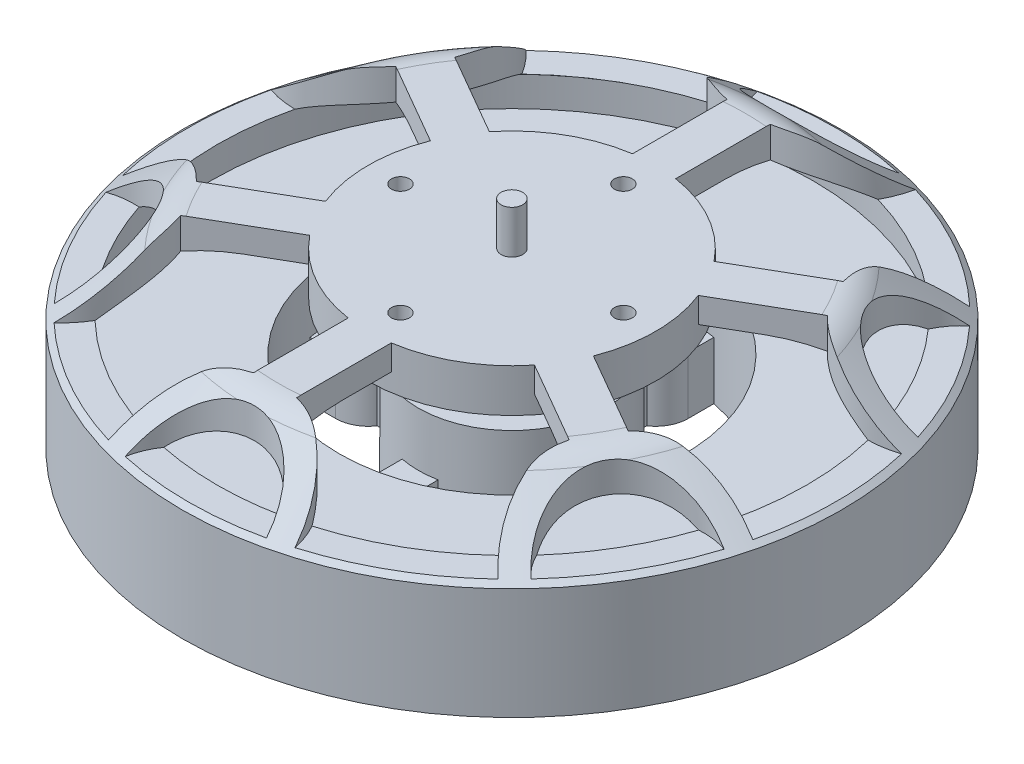
SolidWorks part; units mm, degrees
ref_plane "Front Plane" through (0, 0, 0) normal (0, 0, 1) x (1, 0, 0)
ref_plane "Top Plane" through (0, 0, 0) normal (0, 1, 0) x (1, 0, 0)
ref_plane "Right Plane" through (0, 0, 0) normal (1, 0, 0) x (0, 0, -1)
ref_plane "Plane1" through (0, 0, 0) normal (-0.7071, 0, 0.7071) x (0.7071, 0, 0.7071)
ref_axis "Axis1" through (0, 40.089, 0) along (0, -1, 0)
sketch "Sketch1" plane through (0, 0, 0) normal (0, 0, 1) x (1, 0, 0)
  line L0 (0, 0) -> (9.65, 0)
  line L1 (9.65, 0) -> (9.65, 3.93)
  line L2 (9.65, 3.93) -> (27.5, 3.93)
  line L3 (27.5, 3.93) -> (45.83, 8.08)
  line L4 (45.83, 8.08) -> (45.83, 23.58)
  line L5 (45.83, 23.58) -> (36.1322, 30.9557)
  line L6 (32.5, 32.18) -> (1.5, 32.18)
  line L7 (1.5, 32.18) -> (1.5, 38.18)
  line L8 (1.5, 38.18) -> (0, 38.18)
  line L9 (0, 38.18) -> (0, 0) construction
  line L10 (0, 0) -> (0, 38.18)
  arc A0 (36.1322, 30.9557) -> (32.5, 32.18) centre (32.5, 26.18) ccw
  dimension "D10" = 6
  dimension "D1" = 3
  dimension "D2" = 6
  dimension "D3" = 28.25
  dimension "D4" = 3.93
  dimension "D5" = 19.3
  dimension "D6" = 4.15
  dimension "D7" = 91.66
  dimension "D8" = 55
  dimension "D9" = 65
  dimension "D11" = 15.5
revolve "Revolve1" add sketch "Sketch1" angle 360 about L9
sketch "Sketch2" plane through (0, 3.93, 0) normal (0, -1, 0) x (1, 0, 0)
  line L0 (0, 0) -> (0, 27.5) construction
  line L1 (2.5, 12.7574) -> (2.5, 16.2583)
  line L2 (4.5, 20) -> (4.5, 23.5744)
  line L3 (0, 0) -> (16.9706, 16.9706) construction
  line L4 (20, 4.5) -> (23.5744, 4.5)
  line L5 (12.7574, 2.5) -> (16.2583, 2.5)
  line L6 (20, -4.5) -> (23.5744, -4.5)
  line L7 (4.5, -20) -> (4.5, -23.5744)
  line L8 (2.5, -12.7574) -> (2.5, -16.2583)
  line L9 (12.7574, -2.5) -> (16.2583, -2.5)
  line L10 (-4.5, -20) -> (-4.5, -23.5744)
  line L11 (-20, -4.5) -> (-23.5744, -4.5)
  line L12 (-12.7574, -2.5) -> (-16.2583, -2.5)
  line L13 (-2.5, -12.7574) -> (-2.5, -16.2583)
  line L14 (-20, 4.5) -> (-23.5744, 4.5)
  line L15 (-4.5, 20) -> (-4.5, 23.5744)
  line L16 (-2.5, 12.7574) -> (-2.5, 16.2583)
  line L17 (-12.7574, 2.5) -> (-16.2583, 2.5)
  arc A0 (4.5, 23.5744) -> (23.5744, 4.5) centre (0, 0) cw
  arc A1 (4.5, 20) -> (2.5, 16.2583) centre (0, 20) cw
  arc A2 (2.5, 12.7574) -> (12.7574, 2.5) centre (0, 0) cw
  circle A3 centre (0, 0) radius 27.5 construction
  arc A4 (20, 4.5) -> (16.2583, 2.5) centre (20, 0) ccw
  arc A5 (20, -4.5) -> (16.2583, -2.5) centre (20, 0) cw
  arc A6 (23.5744, -4.5) -> (4.5, -23.5744) centre (0, 0) cw
  arc A7 (4.5, -20) -> (2.5, -16.2583) centre (0, -20) ccw
  arc A8 (12.7574, -2.5) -> (2.5, -12.7574) centre (0, 0) cw
  arc A9 (-4.5, -20) -> (-2.5, -16.2583) centre (0, -20) cw
  arc A10 (-4.5, -23.5744) -> (-23.5744, -4.5) centre (0, 0) cw
  arc A11 (-20, -4.5) -> (-16.2583, -2.5) centre (-20, 0) ccw
  arc A12 (-2.5, -12.7574) -> (-12.7574, -2.5) centre (0, 0) cw
  arc A13 (-20, 4.5) -> (-16.2583, 2.5) centre (-20, 0) cw
  arc A14 (-23.5744, 4.5) -> (-4.5, 23.5744) centre (0, 0) cw
  arc A15 (-4.5, 20) -> (-2.5, 16.2583) centre (0, 20) ccw
  arc A16 (-12.7574, 2.5) -> (-2.5, 12.7574) centre (0, 0) cw
  point P4 (0, 20)
  point P51 (0, 0)
  dimension "D2" = 13
  dimension "D5" = 24
  dimension "D1" = 20
  dimension "D3" = 5
  dimension "D4" = 9
  dimension "D6" = 45
  dimension "D7" = 4
hole_wizard "M4x0.7 Tapped Hole1" positions "3DSketch1" profile "Sketch4" tap size "M4x0.7" standard "ANSI Metric"
sketch3d "3DSketch1"
  point P0 (-20, 3.93, 0)
  point P3 (0, 3.93, 20)
  point P6 (20, 3.93, 0)
  point P9 (0, 3.93, -20)
sketch "Sketch4" plane through (-20, 3.93, 0) normal (1, 0, 0) x (0, 0, -1)
  line L0 (0, 0) -> (0, 8.9914)
  line L1 (0, 8.9914) -> (1.65, 8)
  line L2 (1.65, 8) -> (1.65, 0)
  line L5 (1.65, 0) -> (0, 0)
  line L10 (0, 8.9914) -> (-1.65, 8) construction
  line L11 (0, -6.35) -> (0, 107.95) construction
  dimension "Tap Drill Dia." = 3.3
  dimension "Tap Drill Depth" = 8
  dimension "Drill Angle" = 118
cosmetic thread "Hole Thread1" parameters "D1"=7.874, "D2"=4
cosmetic thread "Hole Thread2" parameters "D1"=7.874, "D2"=4
cosmetic thread "Hole Thread3" parameters "D1"=7.874, "D2"=4
cosmetic thread "Hole Thread4" parameters "D1"=7.874, "D2"=4
extrude "Cut-Extrude1" cut sketch "Sketch2" against normal blind 8
sketch "Sketch5" plane through (0, 0, 0) normal (0, 0, 1) x (1, 0, 0)
  line L0 (24, 19.43) -> (41.83, 19.43)
  line L1 (-27.5, 3.93) -> (27.5, 3.93) construction
  line L2 (41.83, 19.43) -> (41.83, 23.58)
  line L3 (45.83, 8.08) -> (45.83, 23.58) construction
  line L4 (10, 19.43) -> (13, 19.43)
  line L5 (13, 19.43) -> (13, 11.93)
  line L6 (13, 11.93) -> (24, 11.93)
  line L7 (24, 11.93) -> (24, 19.43)
  line L8 (0, 40.089) -> (0, -1.909) construction
  line L9 (4.5, 11.93) -> (23.5744, 11.93) construction
  line L10 (45.83, 23.58) -> (-45.83, 23.58) construction
  line L11 (20, 28.68) -> (26.6996, 28.68)
  line L12 (32.5, 32.18) -> (-32.5, 32.18) construction
  line L13 (41.83, 23.58) -> (45.83, 20.5378) construction
  line L14 (45.83, 23.58) -> (36.1322, 30.9557) construction
  line L15 (20, 28.68) -> (20, 26.18)
  line L16 (20, 26.18) -> (10, 26.18)
  line L17 (10, 26.18) -> (10, 19.43)
  arc A0 (26.6996, 28.68) -> (41.83, 23.58) centre (26.6996, 3.6861) cw
  dimension "D1" = 15.5
  dimension "D2" = 4
  dimension "D3" = 13
  dimension "D4" = 24
  dimension "D5" = 3.5
  dimension "D6" = 20
  dimension "D7" = 6
  dimension "D8" = 10
revolve "Cut-Revolve3" cut sketch "Sketch5" angle 360 about axis through (0, 40.089, 0) along (0, -1, 0)
sketch "Sketch6" plane through (0, 0, 0) normal (0, 1, 0) x (1, 0, 0)
  line L0 (-3, 19.7737) -> (-3, 32.9241)
  line L1 (3, 19.7737) -> (3, 32.9241)
  line L2 (-3, 19.7737) -> (3, 19.7737) construction
  line L3 (0, 45.83) -> (0, 35.83) construction
  line L4 (15.6245, 12.4849) -> (27.0131, 19.0601)
  line L5 (18.6245, 7.2888) -> (30.0131, 13.864)
  line L6 (15.6245, 12.4849) -> (18.6245, 7.2888) construction
  line L7 (39.6899, 22.915) -> (31.0297, 17.915) construction
  line L8 (18.6245, -7.2888) -> (30.0131, -13.864)
  line L9 (15.6245, -12.4849) -> (27.0131, -19.0601)
  line L10 (18.6245, -7.2888) -> (15.6245, -12.4849) construction
  line L11 (39.6899, -22.915) -> (31.0297, -17.915) construction
  line L12 (3, -19.7737) -> (3, -32.9241)
  line L13 (-3, -19.7737) -> (-3, -32.9241)
  line L14 (3, -19.7737) -> (-3, -19.7737) construction
  line L15 (0, -45.83) -> (0, -35.83) construction
  line L16 (-15.6245, -12.4849) -> (-27.0131, -19.0601)
  line L17 (-18.6245, -7.2888) -> (-30.0131, -13.864)
  line L18 (-15.6245, -12.4849) -> (-18.6245, -7.2888) construction
  line L19 (-39.6899, -22.915) -> (-31.0297, -17.915) construction
  line L20 (-18.6245, 7.2888) -> (-30.0131, 13.864)
  line L21 (-15.6245, 12.4849) -> (-27.0131, 19.0601)
  line L22 (-18.6245, 7.2888) -> (-15.6245, 12.4849) construction
  line L23 (-39.6899, 22.915) -> (-31.0297, 17.915) construction
  line L24 (0, 15.5) -> (15.5, 0) construction
  line L25 (15.5, 0) -> (0, -15.5) construction
  line L26 (0, -15.5) -> (-15.5, 0) construction
  line L27 (-15.5, 0) -> (0, 15.5) construction
  arc A1 (-9.9403, 44.739) -> (9.9403, 44.739) centre (0, 45.83) ccw
  circle A2 centre (0, 0) radius 45.83 construction
  arc A3 (-13.1108, 43.9146) -> (-3, 32.9241) centre (0, 45.83) ccw
  arc A4 (13.1108, 43.9146) -> (3, 32.9241) centre (0, 45.83) cw
  arc A5 (-13.1108, 43.9146) -> (-9.9403, 44.739) centre (0, 0) cw
  arc A6 (9.9403, 44.739) -> (13.1108, 43.9146) centre (0, 0) cw
  arc A7 (33.775, 30.9781) -> (43.7153, 13.7609) centre (39.6899, 22.915) ccw
  arc A8 (31.4758, 33.3116) -> (27.0131, 19.0601) centre (39.6899, 22.915) ccw
  arc A9 (44.5866, 10.603) -> (30.0131, 13.864) centre (39.6899, 22.915) cw
  arc A10 (31.4758, 33.3116) -> (33.775, 30.9781) centre (0, 0) cw
  arc A11 (43.7153, 13.7609) -> (44.5866, 10.603) centre (0, 0) cw
  arc A12 (43.7153, -13.7609) -> (33.775, -30.9781) centre (39.6899, -22.915) ccw
  arc A13 (44.5866, -10.603) -> (30.0131, -13.864) centre (39.6899, -22.915) ccw
  arc A14 (31.4758, -33.3116) -> (27.0131, -19.0601) centre (39.6899, -22.915) cw
  arc A15 (44.5866, -10.603) -> (43.7153, -13.7609) centre (0, 0) cw
  arc A16 (33.775, -30.9781) -> (31.4758, -33.3116) centre (0, 0) cw
  arc A17 (9.9403, -44.739) -> (-9.9403, -44.739) centre (0, -45.83) ccw
  arc A18 (13.1108, -43.9146) -> (3, -32.9241) centre (0, -45.83) ccw
  arc A19 (-13.1108, -43.9146) -> (-3, -32.9241) centre (0, -45.83) cw
  arc A20 (13.1108, -43.9146) -> (9.9403, -44.739) centre (0, 0) cw
  arc A21 (-9.9403, -44.739) -> (-13.1108, -43.9146) centre (0, 0) cw
  arc A22 (-33.775, -30.9781) -> (-43.7153, -13.7609) centre (-39.6899, -22.915) ccw
  arc A23 (-31.4758, -33.3116) -> (-27.0131, -19.0601) centre (-39.6899, -22.915) ccw
  arc A24 (-44.5866, -10.603) -> (-30.0131, -13.864) centre (-39.6899, -22.915) cw
  arc A25 (-31.4758, -33.3116) -> (-33.775, -30.9781) centre (0, 0) cw
  arc A26 (-43.7153, -13.7609) -> (-44.5866, -10.603) centre (0, 0) cw
  arc A27 (-43.7153, 13.7609) -> (-33.775, 30.9781) centre (-39.6899, 22.915) ccw
  arc A28 (-44.5866, 10.603) -> (-30.0131, 13.864) centre (-39.6899, 22.915) ccw
  arc A29 (-31.4758, 33.3116) -> (-27.0131, 19.0601) centre (-39.6899, 22.915) cw
  arc A30 (-44.5866, 10.603) -> (-43.7153, 13.7609) centre (0, 0) cw
  arc A31 (-33.775, 30.9781) -> (-31.4758, 33.3116) centre (0, 0) cw
  arc A32 (3, 19.7737) -> (15.6245, 12.4849) centre (0, 0) cw
  arc A33 (18.6245, 7.2888) -> (18.6245, -7.2888) centre (0, 0) cw
  arc A34 (15.6245, -12.4849) -> (3, -19.7737) centre (0, 0) cw
  arc A35 (-3, -19.7737) -> (-15.6245, -12.4849) centre (0, 0) cw
  arc A36 (-18.6245, -7.2888) -> (-18.6245, 7.2888) centre (0, 0) cw
  arc A37 (-3, 19.7737) -> (-15.6245, 12.4849) centre (0, 0) ccw
  point P0 (0, 19.7737)
  point P17 (0, 15.5)
  point P28 (15.5, 0)
  point P38 (0, -15.5)
  point P68 (0, 0)
  point P69 (-15.5, 0)
  dimension "D1" = 6
  dimension "D3" = 3.25
  dimension "D5" = 20
  dimension "D2" = 6
  dimension "D4" = 10
  dimension "D6" = 15.5
extrude "Cut-Extrude3" cut sketch "Sketch6" against normal blind 8 from surface at 32.18 flip side to cut starting at face at (0, 32.18, 1.5)
hole_wizard "M3x0.5 Tapped Hole1" positions "Sketch8" profile "Sketch10" tap size "M3x0.5" standard "ANSI Metric" end condition up to next
sketch "Sketch8" plane through (0, 32.18, 0) normal (0, 1, 0) x (1, 0, 0)
  point P0 (0, 15.5)
  point P3 (15.5, 0)
  point P6 (0, -15.5)
  point P9 (-15.5, 0)
sketch "Sketch10" plane through (0, 32.18, -15.5) normal (1, 0, 0) x (0, 0, 1)
  line L0 (0, 0) -> (0, 6)
  line L1 (0, 6) -> (1.25, 6)
  line L2 (1.25, 6) -> (1.25, 0)
  line L5 (1.25, 0) -> (0, 0)
  line L11 (0, -6.35) -> (0, 107.95) construction
  dimension "Thru Tap Drill Dia." = 2.5
  dimension "Thru Tap Drill Depth" = 6
cosmetic thread "Hole Thread5" parameters "D2"=3
cosmetic thread "Hole Thread6" parameters "D2"=3
cosmetic thread "Hole Thread7" parameters "D2"=3
cosmetic thread "Hole Thread8" parameters "D2"=3
sketch "Sketch11" plane through (0, 0, 0) normal (0, 1, 0) x (1, 0, 0)
  line L0 (-26.0427, 21.4465) -> (-21.4465, 26.0427) construction
  line L1 (-27.9873, 23.3911) -> (-23.3911, 27.9873)
  line L2 (-24.0982, 19.502) -> (-19.502, 24.0982)
  line L3 (-23.7446, 23.7446) -> (0, 0) construction
  line L4 (-20, 0) -> (0, 20) construction
  line L5 (-27.9873, 19.502) -> (-19.502, 27.9873) construction
  line L6 (-25.6892, 25.6892) -> (-32.4067, 32.4067) construction
  arc A0 (-27.9873, 23.3911) -> (-24.0982, 19.502) centre (-26.0427, 21.4465) ccw
  arc A1 (-19.502, 24.0982) -> (-23.3911, 27.9873) centre (-21.4465, 26.0427) ccw
  arc A2 (3, 19.7737) -> (-3, 19.7737) centre (0, 0) ccw construction
  circle A3 centre (0, 0) radius 45.83 construction
  point P2 (-23.7446, 23.7446)
  dimension "D1" = 12
  dimension "D2" = 5.5
  dimension "D3" = 9.5
extrude "Boss-Extrude1" add sketch "Sketch11" against normal blind 19.05 from offset 12.7
equation "\"INTERIOR_STATOR_BORE_OD\"= 48MM"
equation "\"INTERIOR_STATOR_BORE_ID\"= 26mm"
equation "\"D5@Sketch2\"=\"INTERIOR_STATOR_BORE_OD\"/2"
equation "\"D2@Sketch2\"=\"INTERIOR_STATOR_BORE_ID\"/2"
equation "\"D3@Sketch5\"=\"INTERIOR_STATOR_BORE_ID\"/2"
equation "\"D4@Sketch5\"=\"INTERIOR_STATOR_BORE_OD\"/2"
